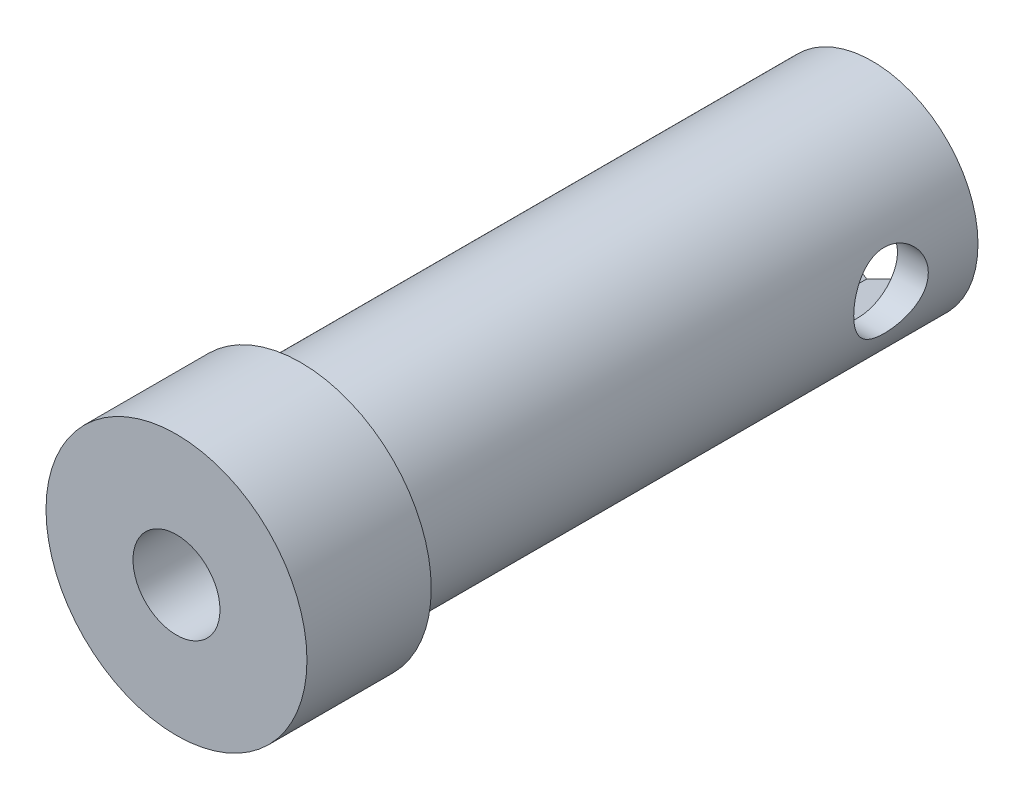
SolidWorks part; units mm, degrees
ref_plane "Front Plane" through (0, 0, 0) normal (0, 0, 1) x (1, 0, 0)
ref_plane "Top Plane" through (0, 0, 0) normal (0, 1, 0) x (1, 0, 0)
ref_plane "Right Plane" through (0, 0, 0) normal (1, 0, 0) x (0, 0, -1)
sketch "Sketch1" plane through (0, 0, 0) normal (0, 0, 1) x (1, 0, 0)
  circle A2 centre (0, 0) radius 4.25
extrude "Boss-Extrude1" add sketch "Sketch1" along normal blind 23
sketch "Sketch2" plane through (0, 0, 23) normal (0, 0, 1) x (1, 0, 0)
  circle A0 centre (0, 0) radius 5.25
extrude "Boss-Extrude2" add sketch "Sketch2" along normal blind 5
ref_plane "Plane1" through (4.25, 0, 0) normal (1, 0, 0) x (0, 0, -1)
sketch "Sketch6" plane through (4.25, 0, 0) normal (1, 0, 0) x (0, 0, -1)
  circle A0 centre (-3.5, 0) radius 1.5
extrude "Cut-Extrude3" cut sketch "Sketch6" against normal blind 2
sketch "Sketch7" plane through (0, 0, 28) normal (0, 0, 1) x (1, 0, 0)
  circle A0 centre (0, 0) radius 1.75
extrude "Cut-Extrude4" cut sketch "Sketch7" against normal through all
sketch "Sketch8" plane through (0, 0, 0) normal (0, 0, -1) x (-1, 0, 0)
  line L1 (-0.2279, 3.4566) -> (-3.1075, 1.5309)
  line L2 (-3.1075, 1.5309) -> (-2.8795, -1.9257)
  line L3 (-2.8795, -1.9257) -> (0.2279, -3.4566)
  line L4 (0.2279, -3.4566) -> (3.1075, -1.5309)
  line L5 (3.1075, -1.5309) -> (2.8795, 1.9257)
  line L6 (2.8795, 1.9257) -> (-0.2279, 3.4566)
  circle A0 centre (0, 0) radius 3 construction
  dimension "D1" = 6
extrude "Cut-Extrude5" cut sketch "Sketch8" against normal blind 4
